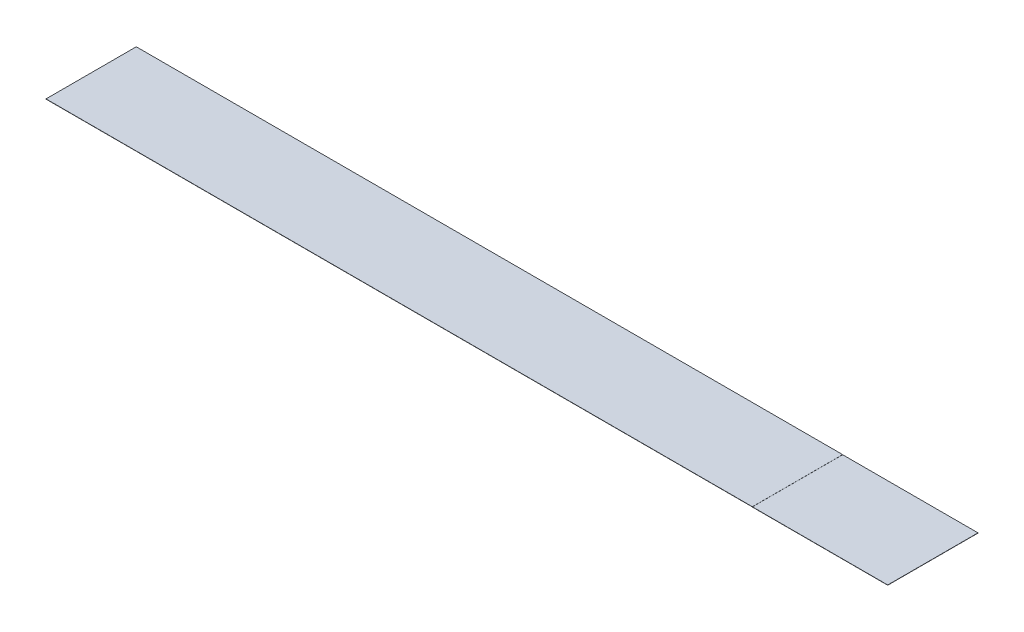
SolidWorks part; units mm, degrees
material "Generic Carbon Fiber"
ref_plane "Front Plane" through (0, 0, 0) normal (0, 0, 1) x (1, 0, 0)
ref_plane "Top Plane" through (0, 0, 0) normal (0, 1, 0) x (1, 0, 0)
ref_plane "Right Plane" through (0, 0, 0) normal (1, 0, 0) x (0, 0, -1)
sketch "Sketch1" plane through (0, 0, 0) normal (0, 1, 0) x (1, 0, 0)
  line L1 (-264.4, 30.5) -> (264.4, 30.5)
  line L2 (-264.4, 30.5) -> (-264.4, -30.5)
  line L3 (-264.4, -30.5) -> (264.4, -30.5)
  line L4 (264.4, 30.5) -> (264.4, -30.5)
  line L5 (-264.4, 30.5) -> (264.4, -30.5) construction
  line L6 (-264.4, -30.5) -> (264.4, 30.5) construction
  point P0 (0, 0)
  dimension "D1" = 528.8
  dimension "D2" = 61
extrude "Extrude1" add sketch "Sketch1" along normal blind 0.15
sketch "Sketch3" plane through (0, 0.15, 0) normal (0, 1, 0) x (1, 0, 0)
  line L0 (-264.4, -30.5) -> (264.4, -30.5) construction
  line L1 (-264.4, 30.5) -> (-284.4, 30.5)
  line L2 (-264.4, 30.5) -> (-264.4, -30.5)
  line L3 (-264.4, -30.5) -> (-284.4, -30.5)
  line L4 (-284.4, 30.5) -> (-284.4, -30.5)
  line L6 (264.4, 30.5) -> (284.4, 30.5)
  line L7 (264.4, 30.5) -> (264.4, -30.5)
  line L8 (264.4, -30.5) -> (284.4, -30.5)
  line L9 (284.4, 30.5) -> (284.4, -30.5)
  dimension "D1" = 20
  dimension "D2" = 20
extrude "Boss-Extrude2" add sketch "Sketch3" against normal up to surface (0.15 mm away) up to face at (0, 0, 0)
sketch "Sketch4" plane through (0, 0, 30.5) normal (0, 0, 1) x (1, 0, 0)
  line L1 (192.95, 0) -> (284.4, 0)
  line L2 (192.95, 0) -> (192.95, -0.0686)
  line L3 (192.95, -0.0686) -> (284.4, -0.0686)
  line L4 (284.4, 0) -> (284.4, -0.0686)
  dimension "D1" = 91.45
  dimension "D2" = 0.0686
extrude "Boss-Extrude3" add sketch "Sketch4" against normal up to surface (61 mm away) up to face at (0, 0.075, -30.5)
sketch "Sketch5" plane through (0, 0, -30.5) normal (0, 0, -1) x (-1, 0, 0)
  line L1 (-284.4, 0.15) -> (-192.95, 0.15)
  line L2 (-284.4, 0.15) -> (-284.4, 0.0814)
  line L3 (-284.4, 0.0814) -> (-192.95, 0.0814)
  line L4 (-192.95, 0.15) -> (-192.95, 0.0814)
  dimension "D1" = 91.45
  dimension "D2" = 0.0686
extrude "Cut-Extrude1" cut sketch "Sketch5" against normal through all
